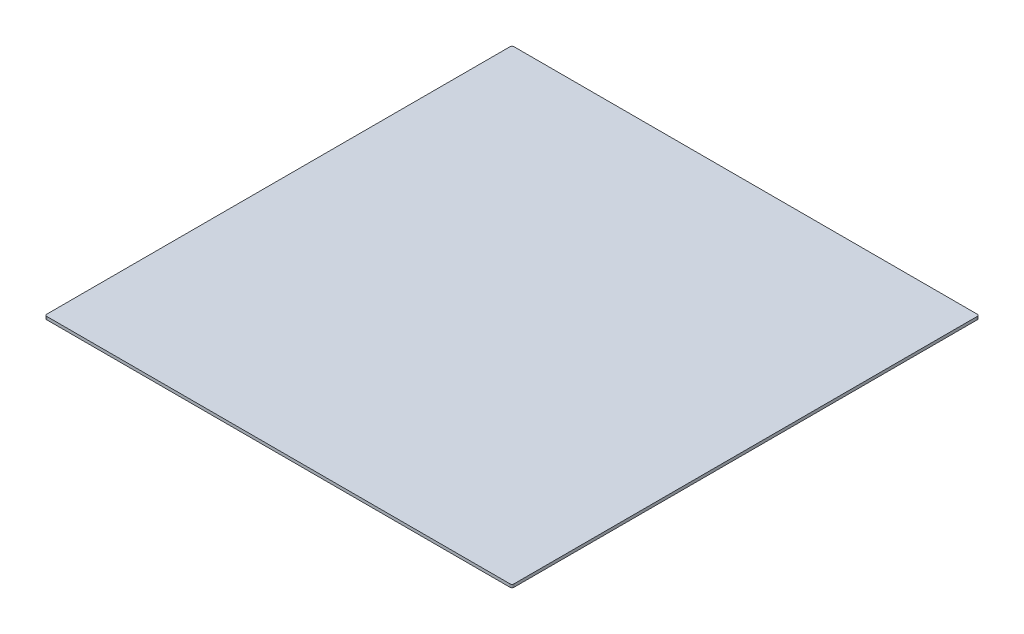
SolidWorks part; units mm, degrees
ref_plane "Front Plane" through (0, 0, 0) normal (0, 0, 1) x (1, 0, 0)
ref_plane "Top Plane" through (0, 0, 0) normal (0, 1, 0) x (1, 0, 0)
ref_plane "Right Plane" through (0, 0, 0) normal (1, 0, 0) x (0, 0, -1)
sketch "Sketch2" plane through (0, 0, 0) normal (0, 1, 0) x (1, 0, 0)
  line L1 (-232.5, -234.5) -> (232.5, -234.5)
  line L2 (-234.5, -232.5) -> (-234.5, 232.5)
  line L3 (-232.5, 234.5) -> (232.5, 234.5)
  line L4 (234.5, -232.5) -> (234.5, 232.5)
  line L5 (-234.5, -234.5) -> (234.5, 234.5) construction
  line L6 (-234.5, 234.5) -> (234.5, -234.5) construction
  arc A0 (232.5, -234.5) -> (234.5, -232.5) centre (232.5, -232.5) ccw
  arc A1 (-232.5, -234.5) -> (-234.5, -232.5) centre (-232.5, -232.5) cw
  arc A2 (-234.5, 232.5) -> (-232.5, 234.5) centre (-232.5, 232.5) cw
  arc A3 (232.5, 234.5) -> (234.5, 232.5) centre (232.5, 232.5) cw
  point P0 (0, 0)
  dimension "D3" = 2
  dimension "D1" = 469
  dimension "D2" = 469
extrude "Boss-Extrude1" add sketch "Sketch2" along normal blind 3
